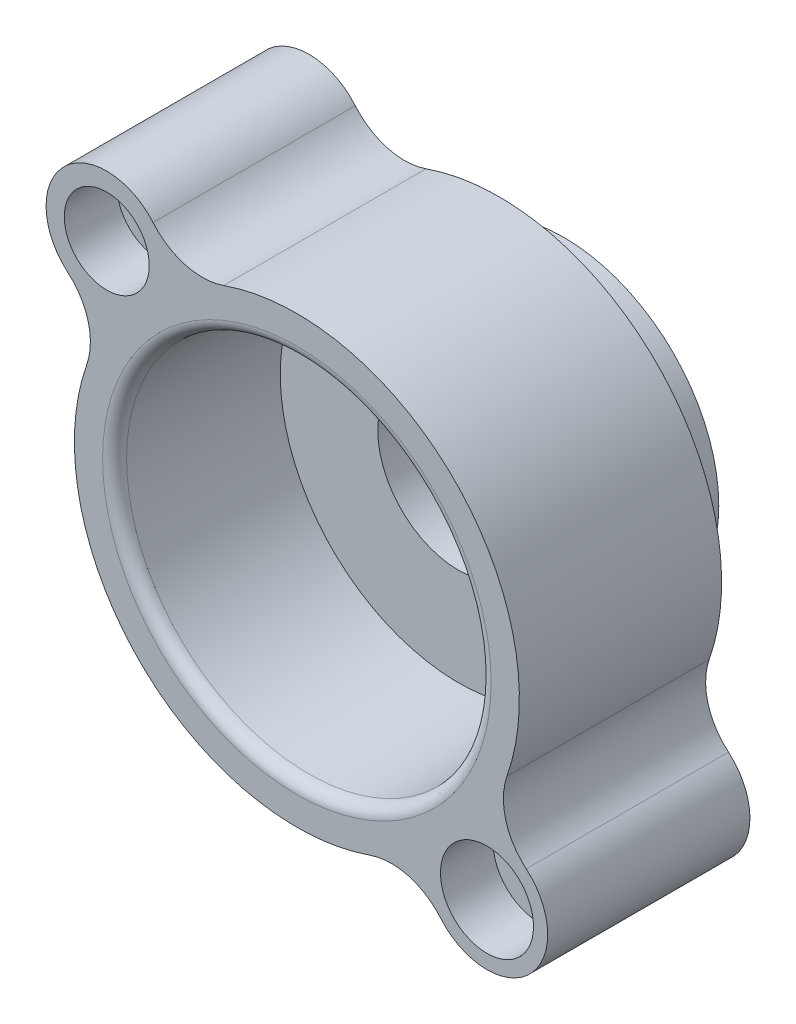
SolidWorks part; units mm, degrees
ref_plane "FRONT" through (0, 0, 0) normal (0, 0, 1) x (1, 0, 0)
ref_plane "TOP" through (0, 0, 0) normal (0, 1, 0) x (1, 0, 0)
ref_plane "RIGHT" through (0, 0, 0) normal (1, 0, 0) x (0, 0, -1)
ref_plane "Plan1" through (0, 0, 838.2) normal (0, 0, 1) x (1, 0, 0)
sketch "Esquisse1" plane through (0, 0, 838.2) normal (0, 0, 1) x (1, 0, 0)
  arc A0 (-720.1018, 451.6018) -> (-659.6259, 229.7738) centre (-851.517, 296.617) cw
  arc A1 (-659.6259, 229.7738) -> (229.7738, -659.6259) centre (0, 0) ccw
  arc A2 (229.7738, -659.6259) -> (451.6018, -720.1018) centre (296.617, -851.517) cw
  arc A3 (451.6018, -720.1018) -> (720.1018, -451.6018) centre (596.9, -596.9) ccw
  arc A4 (720.1018, -451.6018) -> (659.6259, -229.7738) centre (851.517, -296.617) cw
  arc A5 (659.6259, -229.7738) -> (-229.7738, 659.6259) centre (0, 0) ccw
  arc A6 (-229.7738, 659.6259) -> (-451.6018, 720.1018) centre (-296.617, 851.517) cw
  arc A7 (-451.6018, 720.1018) -> (-720.1018, 451.6018) centre (-596.9, 596.9) ccw
extrude "Boss.-Extru.1" add sketch "Esquisse1" against normal blind 635
sketch "Esquisse2" plane through (0, 0, 203.2) normal (0, 0, -1) x (-1, 0, 0)
  circle A0 centre (0, 0) radius 486.41
extrude "Boss.-Extru.2" add sketch "Esquisse2" along normal blind 203.2
sketch "Esquisse3" plane through (0, 0, 838.2) normal (0, 0, 1) x (1, 0, 0)
  circle A0 centre (0, 0) radius 572.77
extrude "Enlèv. mat.-Extru.1" cut sketch "Esquisse3" against normal blind 508 draft 1.432
sketch "Esquisse4" plane through (0, 0, 330.2) normal (0, 0, 1) x (1, 0, 0)
  circle A0 centre (0, 0) radius 254
extrude "Enlèv. mat.-Extru.2" cut sketch "Esquisse4" against normal through all
hole_wizard "Perçage1" positions "Esquisse6" profile "Esquisse5" legacy
sketch "Esquisse6" plane through (0, 0, 838.2) normal (0, 0, 1) x (1, 0, 0)
  point P0 (-596.9, 596.9)
sketch "Esquisse5" plane through (-596.9, 596.9, 838.2) normal (1, 0, 0) x (0, -1, 0)
  line L0 (0, 0) -> (0, 838.2)
  line L1 (0, 838.2) -> (69.85, 838.2)
  line L2 (69.85, 838.2) -> (69.85, 165.1)
  line L3 (69.85, 165.1) -> (133.35, 165.1)
  line L4 (133.35, 165.1) -> (133.35, 0)
  line L5 (133.35, 0) -> (0, 0)
  line L6 (0, 110) -> (0, -10) construction
  dimension "Diamètre" = 139.7
  dimension "Profondeur" = 838.2
  dimension "Diamètre chambrage" = 266.7
  dimension "Profondeur chambrage" = 165.1
hole_wizard "Perçage2" positions "Esquisse8" profile "Esquisse7" legacy
sketch "Esquisse8" plane through (0, 0, 838.2) normal (0, 0, 1) x (1, 0, 0)
  point P0 (596.9, -596.9)
sketch "Esquisse7" plane through (596.9, -596.9, 838.2) normal (1, 0, 0) x (0, -1, 0)
  line L0 (0, 0) -> (0, 838.2)
  line L1 (0, 838.2) -> (69.85, 838.2)
  line L2 (69.85, 838.2) -> (69.85, 165.1)
  line L3 (69.85, 165.1) -> (146.05, 165.1)
  line L4 (146.05, 165.1) -> (146.05, 0)
  line L5 (146.05, 0) -> (0, 0)
  line L6 (0, 110) -> (0, -10) construction
  dimension "Diamètre" = 139.7
  dimension "Profondeur" = 838.2
  dimension "Diamètre chambrage" = 292.1
  dimension "Profondeur chambrage" = 165.1
fillet "Congé1" radius 38.1 1 edges at (-572.77, 0, 838.2)
